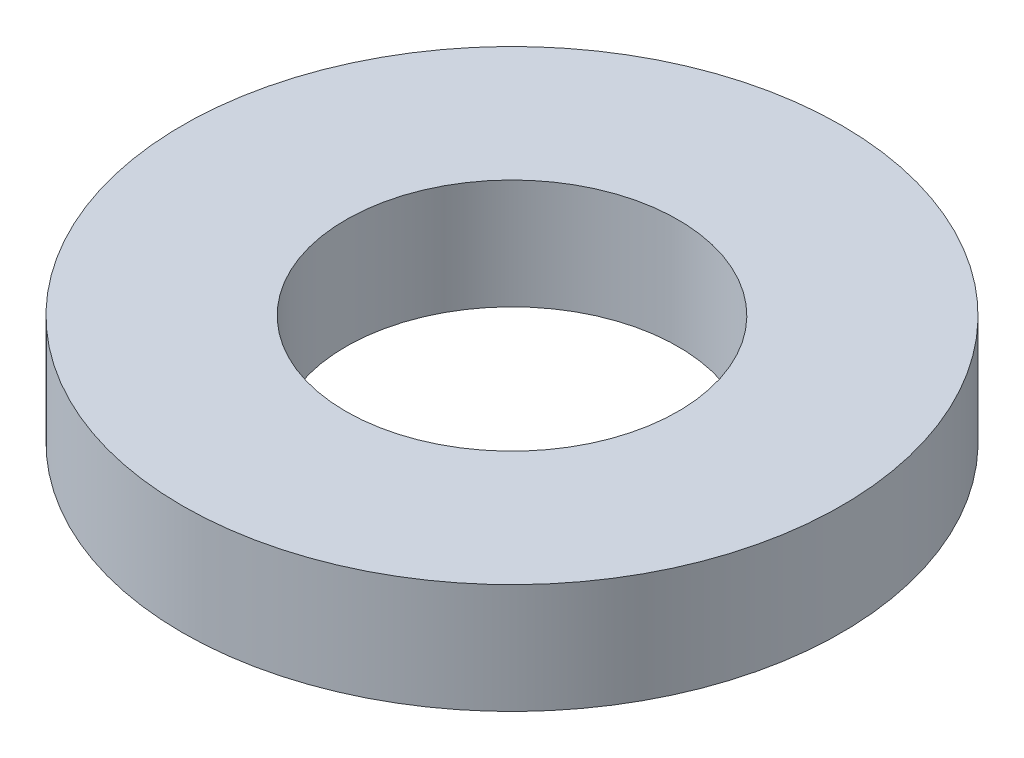
SolidWorks part; units mm, degrees
material "ABS"
ref_plane "Front Plane" through (0, 0, 0) normal (0, 0, 1) x (1, 0, 0)
ref_plane "Top Plane" through (0, 0, 0) normal (0, 1, 0) x (1, 0, 0)
ref_plane "Right Plane" through (0, 0, 0) normal (1, 0, 0) x (0, 0, -1)
sketch "Sketch1" plane through (0, 0, 0) normal (0, 1, 0) x (1, 0, 0)
  circle A0 centre (0, 0) radius 2.3813
  dimension "3/16" = 4.7625
extrude "Boss-Extrude1" add sketch "Sketch1" along normal blind 0.7937
hole_wizard " Clearance Hole1" positions "Sketch2" profile "Sketch3" hole size "M2" standard "ANSI Metric" end condition through all
sketch "Sketch2" plane through (0, 0.7937, 0) normal (0, 1, 0) x (1, 0, 0)
  point P0 (0, 0)
sketch "Sketch3" plane through (0, 0.7937, 0) normal (1, 0, 0) x (0, 0, 1)
  line L0 (0, 0) -> (0, 0.7937)
  line L1 (0, 0.7937) -> (1.2, 0.7937)
  line L2 (1.2, 0.7937) -> (1.2, 0)
  line L5 (1.2, 0) -> (0, 0)
  line L11 (0, -6.35) -> (0, 107.95) construction
  dimension "Thru Hole Dia." = 2.4
  dimension "Thru Hole Depth" = 0.7937
